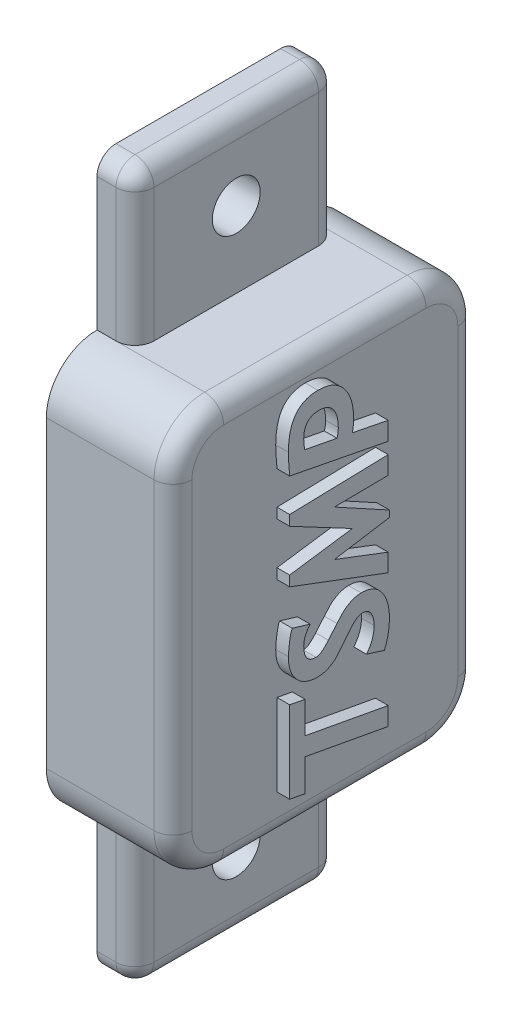
SolidWorks part; units mm, degrees
material "ABS"
ref_plane "X-Y Datum" through (0, 0, 0) normal (0, 0, 1) x (1, 0, 0)
ref_plane "X-Z Datum" through (0, 0, 0) normal (0, 1, 0) x (1, 0, 0)
ref_plane "Y-Z Datum" through (0, 0, 0) normal (1, 0, 0) x (0, 0, -1)
sketch "Sketch1" plane through (0, 0, 0) normal (1, 0, 0) x (0, 0, -1)
  line L1 (10.16, 20.32) -> (-10.16, 20.32)
  line L2 (15.24, 15.24) -> (15.24, -15.24)
  line L3 (10.16, -20.32) -> (-10.16, -20.32)
  line L4 (-15.24, 15.24) -> (-15.24, -15.24)
  line L5 (15.24, 20.32) -> (-15.24, -20.32) construction
  line L6 (15.24, -20.32) -> (-15.24, 20.32) construction
  arc A0 (15.24, -15.24) -> (10.16, -20.32) centre (10.16, -15.24) cw
  arc A1 (10.16, 20.32) -> (15.24, 15.24) centre (10.16, 15.24) cw
  arc A2 (-10.16, 20.32) -> (-15.24, 15.24) centre (-10.16, 15.24) ccw
  arc A3 (-10.16, -20.32) -> (-15.24, -15.24) centre (-10.16, -15.24) cw
  point P0 (0, 0)
  dimension "D3" = 5.08
  dimension "D1" = 40.64
  dimension "D2" = 30.48
extrude "Boss-Extrude1" add sketch "Sketch1" along normal mid plane 12.7
shell "Shell1" thickness 1.27
sketch "Sketch2" plane through (0, -20.32, 0) normal (0, -1, 0) x (1, 0, 0)
  line L0 (-6.35, 10.16) -> (-6.35, -10.16) construction
  line L1 (-6.35, 10.16) -> (-2.54, 10.16)
  line L2 (-6.35, 10.16) -> (-6.35, -10.16)
  line L3 (-6.35, -10.16) -> (-2.54, -10.16)
  line L4 (-2.54, 10.16) -> (-2.54, -10.16)
  line L5 (0, 0) -> (-6.35, 0) construction
  line L6 (6.35, 15.24) -> (-6.35, 15.24) construction
  dimension "D1" = 5.08
  dimension "D2" = 3.81
extrude "Boss-Extrude2" add sketch "Sketch2" along normal blind 15.24
hole_wizard "M4 Clearance Hole1" positions "Sketch6" profile "Sketch7" hole size "M4" standard "ANSI Metric" end condition up to next
sketch "Sketch6" plane through (-2.54, 0, 0) normal (1, 0, 0) x (0, 0, -1)
  line L0 (-10.16, -27.94) -> (0, -27.94) construction
  line L1 (-10.16, -35.56) -> (-10.16, -20.32) construction
  line L2 (0, -27.94) -> (0, -35.56) construction
  line L3 (10.16, -35.56) -> (-10.16, -35.56) construction
  point P0 (0, -27.94)
sketch "Sketch7" plane through (-2.54, -27.94, 0) normal (0, 1, 0) x (0, 0, -1)
  line L0 (0, 0) -> (0, 3.81)
  line L1 (0, 3.81) -> (2.4, 3.81)
  line L2 (2.4, 3.81) -> (2.4, 0)
  line L5 (2.4, 0) -> (0, 0)
  line L11 (0, -6.35) -> (0, 107.95) construction
  dimension "Thru Hole Dia." = 4.8
  dimension "Thru Hole Depth" = 3.81
mirror "Mirror1" about plane through (0, 0, 0) normal (0, 1, 0) of "M4 Clearance Hole1", "Boss-Extrude2"
sketch "Sketch8" plane through (6.35, 0, 0) normal (1, 0, 0) x (0, 0, -1)
  line L0 (5.08, -20.32) -> (5.08, 20.32) construction
  line L3 (10.16, -20.32) -> (-10.16, -20.32) construction
  line L4 (10.16, 20.32) -> (-10.16, 20.32) construction
  line L5 (15.24, -15.24) -> (15.24, 15.24) construction
  text T0 "TSMP" font "Trebuchet MS" height in points 38
  dimension "D1" = 10.16
extrude "Boss-Extrude3" add sketch "Sketch8" along normal blind 1.27
fillet "Fillet1" radius 1.905 18 edges at (6.35, 0, -15.24) (6.35, -20.32, 0) (6.35, 20.32, 0) (6.35, 0, 15.24) (6.35, 18.8321, 13.7521) (6.35, 18.8321, -13.7521) (6.35, -18.8321, -13.7521) (6.35, -18.8321, 13.7521) (-2.54, 27.94, 10.16) (-2.54, 35.56, 0) (-2.54, 27.94, -10.16) (-2.54, -27.94, -10.16) (-2.54, -35.56, 0) (-2.54, -27.94, 10.16) (-4.445, 35.56, 10.16) (-4.445, 35.56, -10.16) (-4.445, -35.56, -10.16) (-4.445, -35.56, 10.16)
